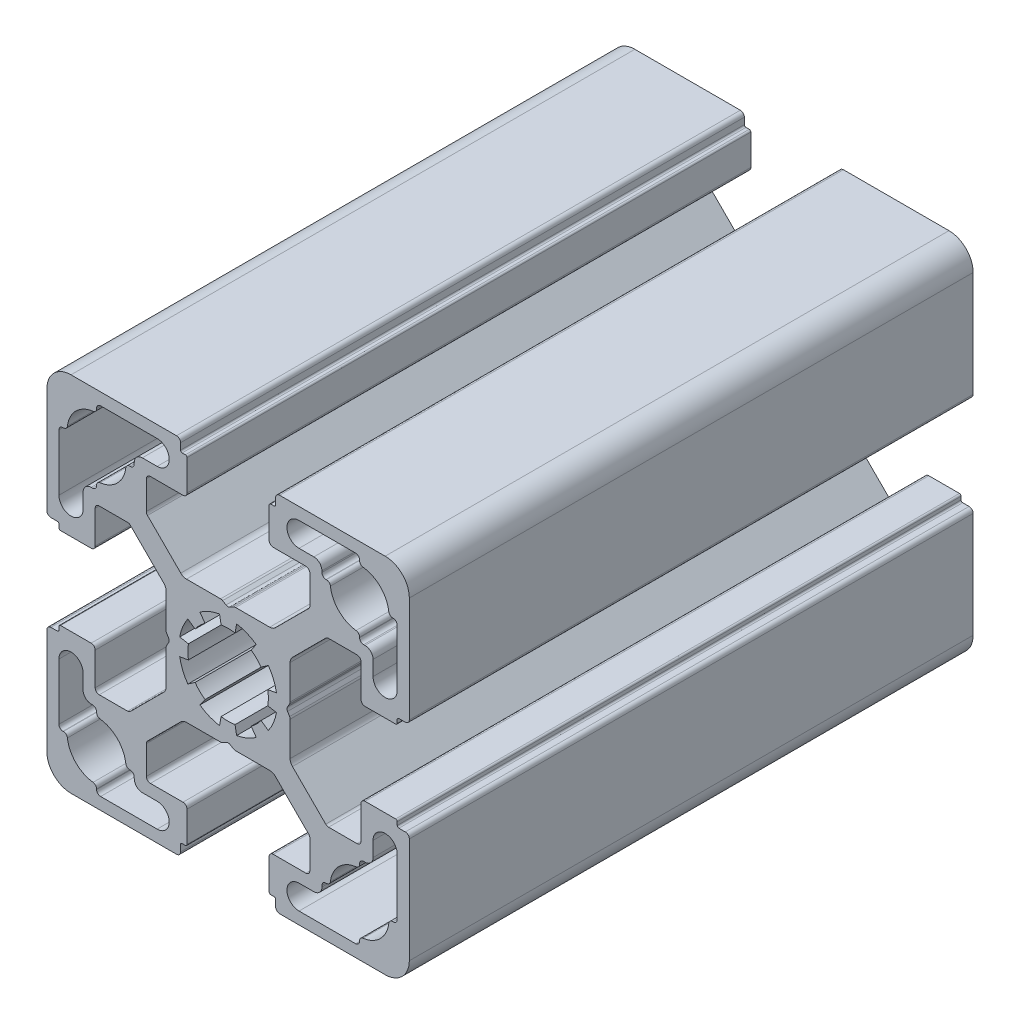
SolidWorks part; units mm, degrees
material "1060 Сплав"
ref_plane "Спереди" through (0, 0, 0) normal (0, 0, 1) x (1, 0, 0)
ref_plane "Сверху" through (0, 0, 0) normal (0, 1, 0) x (1, 0, 0)
ref_plane "Справа" through (0, 0, 0) normal (1, 0, 0) x (0, 0, -1)
sketch "Эскиз1" plane through (0, 0, 0) normal (0, 0, 1) x (1, 0, 0)
  line L0 (-21, 15.825) -> (-21, 8.808)
  line L1 (-15.825, -21) -> (-8.808, -21)
  line L2 (-7.7005, 0.9291) -> (-7.7005, 5.1649)
  line L4 (15.825, 21) -> (8.808, 21)
  line L5 (5.6, 16.5) -> (9.65, 16.5)
  line L6 (16.325, 20.4448) -> (16.325, 20.5)
  line L7 (10.65, 18) -> (8.808, 18)
  line L8 (-7.3858, -0.25) -> (-7.618, -0.6523)
  line L9 (-2.8679, 4.0958) -> (-3.4988, 4.9968)
  line L10 (-16.5, 5.6) -> (-16.5, 9.65)
  line L11 (-16, 10.15) -> (-12.4784, 10.15)
  line L12 (-22, 5.9) -> (-21.2, 5.9)
  line L13 (-20.8, 5.1) -> (-17, 5.1)
  line L14 (-21, 5.7) -> (-21, 5.3)
  line L15 (-22, 5.9) -> (-21.2, 5.9)
  line L16 (4.0958, 2.8679) -> (4.9968, 3.4988)
  line L17 (4.0958, 2.8679) -> (4.9968, 3.4988)
  line L18 (-21, 5.7) -> (-21, 5.3)
  line L19 (-8.1188, 10.2401) -> (-5.8721, 7.9934)
  line L20 (0.9291, 7.7005) -> (5.1649, 7.7005)
  line L21 (-22.5, 6.4) -> (-22.5, 19.5)
  line L22 (10.15, 16) -> (10.15, 12.4784)
  line L23 (0.25, 7.3858) -> (0.6791, 7.6335)
  line L24 (16.325, 12.2052) -> (16.325, 12.15)
  line L25 (-6.4, 22.5) -> (-19.5, 22.5)
  line L26 (16.825, 11.65) -> (17, 11.65)
  line L27 (-10.2401, 8.1188) -> (-12.1249, 10.0036)
  line L28 (-5.7, 21) -> (-5.3, 21)
  line L29 (-7.3858, 0.25) -> (-7.6335, 0.6791)
  line L30 (-0.25, 7.3858) -> (-0.6791, 7.6335)
  line L31 (-5.9, 22) -> (-5.9, 21.2)
  line L32 (-5.7, 21) -> (-5.3, 21)
  line L33 (-5.1, 20.8) -> (-5.1, 17)
  line L34 (-5.9, 22) -> (-5.9, 21.2)
  line L35 (-8.1188, 10.2401) -> (-10.0036, 12.1249)
  line L36 (-5.6, 16.5) -> (-9.65, 16.5)
  line L37 (-10.2401, 8.1188) -> (-7.9934, 5.8721)
  line L38 (18, 10.65) -> (18, 8.808)
  line L39 (-12.2052, 16.325) -> (-12.15, 16.325)
  line L40 (-20.4448, 16.325) -> (-20.5, 16.325)
  line L41 (11.65, 16.825) -> (11.65, 17)
  line L42 (-11.65, 16.825) -> (-11.65, 17)
  line L43 (-18, 10.65) -> (-18, 8.808)
  line L44 (-16.825, 11.65) -> (-17, 11.65)
  line L45 (20.4448, 16.325) -> (20.5, 16.325)
  line L46 (-16.325, 12.2052) -> (-16.325, 12.15)
  line L47 (12.2052, 16.325) -> (12.15, 16.325)
  line L48 (10.2401, 8.1188) -> (7.9934, 5.8721)
  line L49 (0.25, 7.3858) -> (0.6523, 7.618)
  line L50 (-0.9291, 7.7005) -> (-5.1649, 7.7005)
  line L51 (5.6, 16.5) -> (9.65, 16.5)
  line L52 (8.1188, 10.2401) -> (10.0036, 12.1249)
  line L53 (5.9, 22) -> (5.9, 21.2)
  line L54 (5.1, 20.8) -> (5.1, 17)
  line L55 (-0.9291, -7.7005) -> (-5.1649, -7.7005)
  line L56 (5.7, 21) -> (5.3, 21)
  line L57 (5.9, 22) -> (5.9, 21.2)
  line L58 (-0.25, -7.3858) -> (-0.6791, -7.6335)
  line L59 (5.7, 21) -> (5.3, 21)
  line L60 (10.2401, 8.1188) -> (12.1249, 10.0036)
  line L61 (6.4, 22.5) -> (19.5, 22.5)
  line L62 (22.5, 6.4) -> (22.5, 19.5)
  line L63 (-10.15, 16) -> (-10.15, 12.4784)
  line L64 (8.1188, 10.2401) -> (5.8721, 7.9934)
  line L65 (0.25, -7.3858) -> (0.6791, -7.6335)
  line L66 (21, 5.7) -> (21, 5.3)
  line L67 (-0.25, -7.3858) -> (-0.6523, -7.618)
  line L68 (22, 5.9) -> (21.2, 5.9)
  line L69 (21, 5.7) -> (21, 5.3)
  line L70 (20.8, 5.1) -> (17, 5.1)
  line L71 (22, 5.9) -> (21.2, 5.9)
  line L72 (16, 10.15) -> (12.4784, 10.15)
  line L73 (16.5, 5.6) -> (16.5, 9.65)
  line L74 (-0.9291, 7.7005) -> (-5.1649, 7.7005)
  line L75 (2.8679, 4.0958) -> (3.4988, 4.9968)
  line L76 (7.7005, 0.9291) -> (7.7005, 5.1649)
  line L77 (0.9291, -7.7005) -> (5.1649, -7.7005)
  line L78 (21, 15.825) -> (21, 8.808)
  line L79 (-5.6, -16.5) -> (-9.65, -16.5)
  line L80 (-16.325, -20.4448) -> (-16.325, -20.5)
  line L81 (4.0958, -2.8679) -> (4.9968, -3.4988)
  line L82 (2.8679, -4.0958) -> (3.4988, -4.9968)
  line L83 (-10.65, -18) -> (-8.808, -18)
  line L84 (4.0958, -2.8679) -> (4.9968, -3.4988)
  line L85 (2.8679, -4.0958) -> (3.4988, -4.9968)
  line L86 (0.8682, -4.924) -> (1.0593, -6.0073)
  line L87 (0.8682, -4.924) -> (1.0593, -6.0073)
  line L88 (-0.8682, -4.924) -> (-1.0593, -6.0073)
  line L89 (-4.0958, -2.8679) -> (-4.9968, -3.4988)
  line L90 (-0.8682, -4.924) -> (-1.0593, -6.0073)
  line L91 (-4.0958, -2.8679) -> (-4.9968, -3.4988)
  line L92 (21, -15.825) -> (21, -8.808)
  line L93 (2.8679, -4.0958) -> (3.4988, -4.9968)
  line L94 (-0.9291, -7.7005) -> (-5.1649, -7.7005)
  line L95 (16.5, -5.6) -> (16.5, -9.65)
  line L96 (16, -10.15) -> (12.4784, -10.15)
  line L97 (22, -5.9) -> (21.2, -5.9)
  line L98 (20.8, -5.1) -> (17, -5.1)
  line L99 (21, -5.7) -> (21, -5.3)
  line L100 (22, -5.9) -> (21.2, -5.9)
  line L101 (21, -5.7) -> (21, -5.3)
  line L102 (8.1188, -10.2401) -> (5.8721, -7.9934)
  line L103 (-7.3858, -0.25) -> (-7.6335, -0.6791)
  line L104 (-10.15, -16) -> (-10.15, -12.4784)
  line L105 (22.5, -6.4) -> (22.5, -19.5)
  line L106 (6.4, -22.5) -> (19.5, -22.5)
  line L107 (10.2401, -8.1188) -> (12.1249, -10.0036)
  line L108 (5.7, -21) -> (5.3, -21)
  line L109 (7.7005, -0.9291) -> (7.7005, -5.1649)
  line L110 (5.9, -22) -> (5.9, -21.2)
  line L111 (5.7, -21) -> (5.3, -21)
  line L112 (7.3858, 0.25) -> (7.618, 0.6523)
  line L113 (5.1, -20.8) -> (5.1, -17)
  line L114 (5.9, -22) -> (5.9, -21.2)
  line L115 (-7.7005, -0.9291) -> (-7.7005, -5.1649)
  line L116 (8.1188, -10.2401) -> (10.0036, -12.1249)
  line L117 (5.6, -16.5) -> (9.65, -16.5)
  line L118 (-0.9291, -7.7005) -> (-5.1649, -7.7005)
  line L119 (0.25, -7.3858) -> (0.6523, -7.618)
  line L120 (10.2401, -8.1188) -> (7.9934, -5.8721)
  line L121 (12.2052, -16.325) -> (12.15, -16.325)
  line L122 (-16.325, -12.2052) -> (-16.325, -12.15)
  line L123 (7.3858, -0.25) -> (7.6335, -0.6791)
  line L124 (20.4448, -16.325) -> (20.5, -16.325)
  line L125 (-16.825, -11.65) -> (-17, -11.65)
  line L126 (-18, -10.65) -> (-18, -8.808)
  line L127 (-11.65, -16.825) -> (-11.65, -17)
  line L128 (11.65, -16.825) -> (11.65, -17)
  line L129 (-20.4448, -16.325) -> (-20.5, -16.325)
  line L130 (-4.0958, 2.8679) -> (-4.9968, 3.4988)
  line L131 (-0.8682, 4.924) -> (-1.0593, 6.0073)
  line L132 (0.8682, 4.924) -> (1.0593, 6.0073)
  line L133 (-10.65, 18) -> (-8.808, 18)
  line L134 (-4.924, -0.8682) -> (-6.0073, -1.0593)
  line L135 (-4.924, 0.8682) -> (-6.0073, 1.0593)
  line L136 (0.8682, -4.924) -> (1.0593, -6.0073)
  line L137 (-0.8682, -4.924) -> (-1.0593, -6.0073)
  line L138 (-2.8679, -4.0958) -> (-3.4988, -4.9968)
  line L139 (-4.0958, -2.8679) -> (-4.9968, -3.4988)
  line L140 (-4.924, -0.8682) -> (-6.0073, -1.0593)
  line L141 (-4.924, 0.8682) -> (-6.0073, 1.0593)
  line L142 (2.8679, 4.0958) -> (3.4988, 4.9968)
  line L143 (4.0958, 2.8679) -> (4.9968, 3.4988)
  line L144 (4.924, 0.8682) -> (6.0073, 1.0593)
  line L145 (4.924, -0.8682) -> (6.0073, -1.0593)
  line L146 (4.0958, -2.8679) -> (4.9968, -3.4988)
  line L147 (2.8679, -4.0958) -> (3.4988, -4.9968)
  line L148 (-16.325, 20.4448) -> (-16.325, 20.5)
  line L149 (-12.2052, -16.325) -> (-12.15, -16.325)
  line L150 (-5.6, 16.5) -> (-9.65, 16.5)
  line L151 (-15.825, 21) -> (-8.808, 21)
  line L152 (18, -10.65) -> (18, -8.808)
  line L153 (-10.2401, -8.1188) -> (-7.9934, -5.8721)
  line L154 (-5.6, -16.5) -> (-9.65, -16.5)
  line L155 (-8.1188, -10.2401) -> (-10.0036, -12.1249)
  line L156 (-5.9, -22) -> (-5.9, -21.2)
  line L157 (-5.1, -20.8) -> (-5.1, -17)
  line L158 (-5.7, -21) -> (-5.3, -21)
  line L159 (-5.9, -22) -> (-5.9, -21.2)
  line L160 (-0.25, -7.3858) -> (-0.6791, -7.6335)
  line L161 (-5.7, -21) -> (-5.3, -21)
  line L162 (-10.2401, -8.1188) -> (-12.1249, -10.0036)
  line L163 (16.825, -11.65) -> (17, -11.65)
  line L164 (-6.4, -22.5) -> (-19.5, -22.5)
  line L165 (16.325, -12.2052) -> (16.325, -12.15)
  line L166 (0.25, -7.3858) -> (0.6791, -7.6335)
  line L167 (10.15, -16) -> (10.15, -12.4784)
  line L168 (7.3858, 0.25) -> (7.6335, 0.6791)
  line L169 (-22.5, -6.4) -> (-22.5, -19.5)
  line L170 (0.9291, -7.7005) -> (5.1649, -7.7005)
  line L171 (7.7005, 0.9291) -> (7.7005, 5.1649)
  line L172 (-8.1188, -10.2401) -> (-5.8721, -7.9934)
  line L173 (-21, -5.7) -> (-21, -5.3)
  line L174 (4.0958, -2.8679) -> (4.9968, -3.4988)
  line L175 (4.0958, -2.8679) -> (4.9968, -3.4988)
  line L176 (4.0958, -2.8679) -> (4.9968, -3.4988)
  line L177 (-22, -5.9) -> (-21.2, -5.9)
  line L178 (-21, -5.7) -> (-21, -5.3)
  line L179 (-20.8, -5.1) -> (-17, -5.1)
  line L180 (-22, -5.9) -> (-21.2, -5.9)
  line L181 (-16, -10.15) -> (-12.4784, -10.15)
  line L182 (-2.8679, -4.0958) -> (-3.4988, -4.9968)
  line L183 (-16.5, -5.6) -> (-16.5, -9.65)
  line L184 (-2.8679, -4.0958) -> (-3.4988, -4.9968)
  line L185 (10.65, -18) -> (8.808, -18)
  line L186 (16.325, -20.4448) -> (16.325, -20.5)
  line L187 (5.6, -16.5) -> (9.65, -16.5)
  line L188 (15.825, -21) -> (8.808, -21)
  line L189 (-21, -15.825) -> (-21, -8.808)
  arc A0 (-2.8679, 4.0958) -> (-4.0958, 2.8679) centre (0, 0) ccw
  arc A1 (-4.9968, 3.4988) -> (-6.0073, 1.0593) centre (0, 0) ccw
  arc A2 (-19.5, 22.5) -> (-22.5, 19.5) centre (-19.5, 19.5) ccw
  arc A3 (-12.1249, 10.0036) -> (-12.4784, 10.15) centre (-12.4784, 9.65) ccw
  arc A4 (-16, 10.15) -> (-16.5, 9.65) centre (-16, 9.65) ccw
  arc A5 (-17, 5.1) -> (-16.5, 5.6) centre (-17, 5.6) ccw
  arc A6 (-22.5, 6.4) -> (-22, 5.9) centre (-22, 6.4) ccw
  arc A7 (-20.8, 5.1) -> (-21, 5.3) centre (-20.8, 5.3) cw
  arc A8 (-21.2, 5.9) -> (-21, 5.7) centre (-21.2, 5.7) cw
  arc A9 (-7.9934, 5.8721) -> (-7.7005, 5.1649) centre (-8.7005, 5.1649) cw
  arc A10 (10.15, 16) -> (9.65, 16.5) centre (9.65, 16) ccw
  arc A11 (8.808, 21) -> (8.808, 18) centre (8.808, 19.5) ccw
  arc A12 (11.65, 17) -> (10.65, 18) centre (10.65, 17) ccw
  arc A13 (16.325, 20.5) -> (15.825, 21) centre (15.825, 20.5) ccw
  arc A14 (16.325, 20.4448) -> (16.7648, 19.9484) centre (16.825, 20.4448) ccw
  arc A15 (12.2052, 16.325) -> (12.7016, 15.8852) centre (12.2052, 15.825) cw
  arc A16 (-7.6335, -0.6791) -> (-7.7005, -0.9291) centre (-7.2005, -0.9291) ccw
  arc A17 (-5.9, 21.2) -> (-5.7, 21) centre (-5.7, 21.2) ccw
  arc A18 (-7.3858, -0.25) -> (-7.3858, 0.25) centre (-7.8188, 0) ccw
  arc A19 (-22.5, 6.4) -> (-22, 5.9) centre (-22, 6.4) ccw
  arc A20 (-21.2, 5.9) -> (-21, 5.7) centre (-21.2, 5.7) cw
  arc A21 (-6.4, 22.5) -> (-5.9, 22) centre (-6.4, 22) cw
  arc A22 (-0.6791, 7.6335) -> (-0.9291, 7.7005) centre (-0.9291, 7.2005) ccw
  arc A23 (12.15, 16.325) -> (11.65, 16.825) centre (12.15, 16.825) cw
  arc A24 (0.25, 7.3858) -> (-0.25, 7.3858) centre (0, 7.8188) cw
  arc A25 (-5.9, 21.2) -> (-5.7, 21) centre (-5.7, 21.2) ccw
  arc A26 (-5.1, 20.8) -> (-5.3, 21) centre (-5.3, 20.8) ccw
  arc A27 (-6.4, 22.5) -> (-5.9, 22) centre (-6.4, 22) cw
  arc A28 (-5.1, 17) -> (-5.6, 16.5) centre (-5.6, 17) cw
  arc A29 (-10.15, 16) -> (-9.65, 16.5) centre (-9.65, 16) cw
  arc A30 (-5.8721, 7.9934) -> (-5.1649, 7.7005) centre (-5.1649, 8.7005) ccw
  arc A31 (-15.8852, 12.7016) -> (-12.7016, 15.8852) centre (-16.325, 16.325) ccw
  arc A32 (-21, 8.808) -> (-18, 8.808) centre (-19.5, 8.808) ccw
  arc A33 (-17, 11.65) -> (-18, 10.65) centre (-17, 10.65) ccw
  arc A34 (-20.5, 16.325) -> (-21, 15.825) centre (-20.5, 15.825) ccw
  arc A35 (-20.4448, 16.325) -> (-19.9484, 16.7648) centre (-20.4448, 16.825) ccw
  arc A36 (-16.325, 12.2052) -> (-15.8852, 12.7016) centre (-15.825, 12.2052) cw
  arc A37 (16.7648, 19.9484) -> (19.9484, 16.7648) centre (16.325, 16.325) cw
  arc A38 (16.325, 12.15) -> (16.825, 11.65) centre (16.825, 12.15) ccw
  arc A39 (19.5, 22.5) -> (22.5, 19.5) centre (19.5, 19.5) cw
  arc A40 (10.0036, 12.1249) -> (10.15, 12.4784) centre (9.65, 12.4784) ccw
  arc A41 (16.325, 12.2052) -> (15.8852, 12.7016) centre (15.825, 12.2052) ccw
  arc A42 (20.4448, 16.325) -> (19.9484, 16.7648) centre (20.4448, 16.825) cw
  arc A43 (0.6791, 7.6335) -> (0.9291, 7.7005) centre (0.9291, 7.2005) cw
  arc A44 (-10.0036, 12.1249) -> (-10.15, 12.4784) centre (-9.65, 12.4784) cw
  arc A45 (20.5, 16.325) -> (21, 15.825) centre (20.5, 15.825) cw
  arc A46 (17, 11.65) -> (18, 10.65) centre (17, 10.65) cw
  arc A47 (21, 8.808) -> (18, 8.808) centre (19.5, 8.808) cw
  arc A48 (0.6791, -7.6335) -> (0.9291, -7.7005) centre (0.9291, -7.2005) ccw
  arc A49 (15.8852, 12.7016) -> (12.7016, 15.8852) centre (16.325, 16.325) cw
  arc A50 (5.8721, 7.9934) -> (5.1649, 7.7005) centre (5.1649, 8.7005) cw
  arc A51 (-0.25, -7.3858) -> (0.25, -7.3858) centre (0, -7.8188) cw
  arc A52 (10.15, 16) -> (9.65, 16.5) centre (9.65, 16) ccw
  arc A53 (5.1, 17) -> (5.6, 16.5) centre (5.6, 17) ccw
  arc A54 (6.4, 22.5) -> (5.9, 22) centre (6.4, 22) ccw
  arc A55 (5.1, 20.8) -> (5.3, 21) centre (5.3, 20.8) cw
  arc A56 (5.9, 21.2) -> (5.7, 21) centre (5.7, 21.2) cw
  arc A57 (6.4, 22.5) -> (5.9, 22) centre (6.4, 22) ccw
  arc A58 (-0.6791, -7.6335) -> (-0.9291, -7.7005) centre (-0.9291, -7.2005) cw
  arc A59 (21.2, 5.9) -> (21, 5.7) centre (21.2, 5.7) ccw
  arc A60 (22.5, 6.4) -> (22, 5.9) centre (22, 6.4) cw
  arc A61 (5.9, 21.2) -> (5.7, 21) centre (5.7, 21.2) cw
  arc A62 (7.9934, 5.8721) -> (7.7005, 5.1649) centre (8.7005, 5.1649) ccw
  arc A63 (21.2, 5.9) -> (21, 5.7) centre (21.2, 5.7) ccw
  arc A64 (20.8, 5.1) -> (21, 5.3) centre (20.8, 5.3) ccw
  arc A65 (22.5, 6.4) -> (22, 5.9) centre (22, 6.4) cw
  arc A66 (17, 5.1) -> (16.5, 5.6) centre (17, 5.6) cw
  arc A67 (7.6335, 0.6791) -> (7.7005, 0.9291) centre (7.2005, 0.9291) ccw
  arc A68 (16, 10.15) -> (16.5, 9.65) centre (16, 9.65) cw
  arc A69 (12.1249, 10.0036) -> (12.4784, 10.15) centre (12.4784, 9.65) cw
  arc A70 (19.5, 22.5) -> (22.5, 19.5) centre (19.5, 19.5) cw
  arc A71 (4.9968, 3.4988) -> (6.0073, 1.0593) centre (0, 0) cw
  arc A72 (7.3858, 0.25) -> (7.3858, -0.25) centre (7.8188, 0) ccw
  arc A73 (2.8679, 4.0958) -> (4.0958, 2.8679) centre (0, 0) cw
  arc A74 (-10.15, -16) -> (-9.65, -16.5) centre (-9.65, -16) ccw
  arc A75 (-8.808, -21) -> (-8.808, -18) centre (-8.808, -19.5) ccw
  arc A76 (-11.65, -17) -> (-10.65, -18) centre (-10.65, -17) ccw
  arc A77 (-16.325, -20.5) -> (-15.825, -21) centre (-15.825, -20.5) ccw
  arc A78 (-16.325, -20.4448) -> (-16.7648, -19.9484) centre (-16.825, -20.4448) ccw
  arc A79 (-12.2052, -16.325) -> (-12.7016, -15.8852) centre (-12.2052, -15.825) cw
  arc A80 (-12.15, -16.325) -> (-11.65, -16.825) centre (-12.15, -16.825) cw
  arc A81 (-16.7648, -19.9484) -> (-19.9484, -16.7648) centre (-16.325, -16.325) cw
  arc A82 (-16.325, -12.15) -> (-16.825, -11.65) centre (-16.825, -12.15) ccw
  arc A83 (-19.5, -22.5) -> (-22.5, -19.5) centre (-19.5, -19.5) cw
  arc A84 (4.0958, -2.8679) -> (2.8679, -4.0958) centre (0, 0) cw
  arc A85 (3.4988, -4.9968) -> (1.0593, -6.0073) centre (0, 0) cw
  arc A86 (0.8682, -4.924) -> (-0.8682, -4.924) centre (0, 0) cw
  arc A87 (-1.0593, -6.0073) -> (-3.4988, -4.9968) centre (0, 0) cw
  arc A88 (3.4988, -4.9968) -> (1.0593, -6.0073) centre (0, 0) cw
  arc A89 (0.8682, -4.924) -> (-0.8682, -4.924) centre (0, 0) cw
  arc A90 (-1.0593, -6.0073) -> (-3.4988, -4.9968) centre (0, 0) cw
  arc A91 (2.8679, -4.0958) -> (4.0958, -2.8679) centre (0, 0) ccw
  arc A92 (7.6335, -0.6791) -> (7.7005, -0.9291) centre (7.2005, -0.9291) cw
  arc A93 (19.5, -22.5) -> (22.5, -19.5) centre (19.5, -19.5) ccw
  arc A94 (12.1249, -10.0036) -> (12.4784, -10.15) centre (12.4784, -9.65) ccw
  arc A95 (16, -10.15) -> (16.5, -9.65) centre (16, -9.65) ccw
  arc A96 (17, -5.1) -> (16.5, -5.6) centre (17, -5.6) ccw
  arc A97 (22.5, -6.4) -> (22, -5.9) centre (22, -6.4) ccw
  arc A98 (20.8, -5.1) -> (21, -5.3) centre (20.8, -5.3) cw
  arc A99 (21.2, -5.9) -> (21, -5.7) centre (21.2, -5.7) cw
  arc A100 (7.9934, -5.8721) -> (7.7005, -5.1649) centre (8.7005, -5.1649) cw
  arc A101 (5.9, -21.2) -> (5.7, -21) centre (5.7, -21.2) ccw
  arc A102 (-7.6335, 0.6791) -> (-7.7005, 0.9291) centre (-7.2005, 0.9291) cw
  arc A103 (22.5, -6.4) -> (22, -5.9) centre (22, -6.4) ccw
  arc A104 (21.2, -5.9) -> (21, -5.7) centre (21.2, -5.7) cw
  arc A105 (6.4, -22.5) -> (5.9, -22) centre (6.4, -22) cw
  arc A106 (5.9, -21.2) -> (5.7, -21) centre (5.7, -21.2) ccw
  arc A107 (5.1, -20.8) -> (5.3, -21) centre (5.3, -20.8) ccw
  arc A108 (6.4, -22.5) -> (5.9, -22) centre (6.4, -22) cw
  arc A109 (5.1, -17) -> (5.6, -16.5) centre (5.6, -17) cw
  arc A110 (10.15, -16) -> (9.65, -16.5) centre (9.65, -16) cw
  arc A111 (5.8721, -7.9934) -> (5.1649, -7.7005) centre (5.1649, -8.7005) ccw
  arc A112 (15.8852, -12.7016) -> (12.7016, -15.8852) centre (16.325, -16.325) ccw
  arc A113 (21, -8.808) -> (18, -8.808) centre (19.5, -8.808) ccw
  arc A114 (-1.0593, 6.0073) -> (-3.4988, 4.9968) centre (0, 0) ccw
  arc A115 (0.8682, 4.924) -> (-0.8682, 4.924) centre (0, 0) ccw
  arc A116 (3.4988, 4.9968) -> (1.0593, 6.0073) centre (0, 0) ccw
  arc A117 (4.0958, 2.8679) -> (2.8679, 4.0958) centre (0, 0) ccw
  arc A118 (4.924, -0.8682) -> (4.924, 0.8682) centre (0, 0) ccw
  arc A119 (6.0073, 1.0593) -> (4.9968, 3.4988) centre (0, 0) ccw
  arc A120 (2.8679, -4.0958) -> (4.0958, -2.8679) centre (0, 0) ccw
  arc A121 (4.9968, -3.4988) -> (6.0073, -1.0593) centre (0, 0) ccw
  arc A122 (-0.8682, -4.924) -> (0.8682, -4.924) centre (0, 0) ccw
  arc A123 (1.0593, -6.0073) -> (3.4988, -4.9968) centre (0, 0) ccw
  arc A124 (-4.0958, -2.8679) -> (-2.8679, -4.0958) centre (0, 0) ccw
  arc A125 (-3.4988, -4.9968) -> (-1.0593, -6.0073) centre (0, 0) ccw
  arc A126 (-4.924, 0.8682) -> (-4.924, -0.8682) centre (0, 0) ccw
  arc A127 (-6.0073, -1.0593) -> (-4.9968, -3.4988) centre (0, 0) ccw
  arc A128 (-19.5, 22.5) -> (-22.5, 19.5) centre (-19.5, 19.5) ccw
  arc A129 (-16.325, 12.15) -> (-16.825, 11.65) centre (-16.825, 12.15) cw
  arc A130 (-16.7648, 19.9484) -> (-19.9484, 16.7648) centre (-16.325, 16.325) ccw
  arc A131 (-12.15, 16.325) -> (-11.65, 16.825) centre (-12.15, 16.825) ccw
  arc A132 (-12.2052, 16.325) -> (-12.7016, 15.8852) centre (-12.2052, 15.825) ccw
  arc A133 (-16.325, 20.4448) -> (-16.7648, 19.9484) centre (-16.825, 20.4448) cw
  arc A134 (-16.325, 20.5) -> (-15.825, 21) centre (-15.825, 20.5) cw
  arc A135 (-11.65, 17) -> (-10.65, 18) centre (-10.65, 17) cw
  arc A136 (-8.808, 21) -> (-8.808, 18) centre (-8.808, 19.5) cw
  arc A137 (-10.15, 16) -> (-9.65, 16.5) centre (-9.65, 16) cw
  arc A138 (17, -11.65) -> (18, -10.65) centre (17, -10.65) ccw
  arc A139 (20.5, -16.325) -> (21, -15.825) centre (20.5, -15.825) ccw
  arc A140 (-10.0036, -12.1249) -> (-10.15, -12.4784) centre (-9.65, -12.4784) ccw
  arc A141 (0.6791, -7.6335) -> (0.9291, -7.7005) centre (0.9291, -7.2005) ccw
  arc A142 (20.4448, -16.325) -> (19.9484, -16.7648) centre (20.4448, -16.825) ccw
  arc A143 (16.325, -12.2052) -> (15.8852, -12.7016) centre (15.825, -12.2052) cw
  arc A144 (10.0036, -12.1249) -> (10.15, -12.4784) centre (9.65, -12.4784) cw
  arc A145 (19.5, -22.5) -> (22.5, -19.5) centre (19.5, -19.5) ccw
  arc A146 (16.325, -12.15) -> (16.825, -11.65) centre (16.825, -12.15) cw
  arc A147 (16.7648, -19.9484) -> (19.9484, -16.7648) centre (16.325, -16.325) ccw
  arc A148 (-16.325, -12.2052) -> (-15.8852, -12.7016) centre (-15.825, -12.2052) ccw
  arc A149 (-20.4448, -16.325) -> (-19.9484, -16.7648) centre (-20.4448, -16.825) cw
  arc A150 (-20.5, -16.325) -> (-21, -15.825) centre (-20.5, -15.825) cw
  arc A151 (-17, -11.65) -> (-18, -10.65) centre (-17, -10.65) cw
  arc A152 (-21, -8.808) -> (-18, -8.808) centre (-19.5, -8.808) cw
  arc A153 (-15.8852, -12.7016) -> (-12.7016, -15.8852) centre (-16.325, -16.325) cw
  arc A154 (-5.8721, -7.9934) -> (-5.1649, -7.7005) centre (-5.1649, -8.7005) cw
  arc A155 (-10.15, -16) -> (-9.65, -16.5) centre (-9.65, -16) ccw
  arc A156 (-5.1, -17) -> (-5.6, -16.5) centre (-5.6, -17) ccw
  arc A157 (-6.4, -22.5) -> (-5.9, -22) centre (-6.4, -22) ccw
  arc A158 (-5.1, -20.8) -> (-5.3, -21) centre (-5.3, -20.8) cw
  arc A159 (-5.9, -21.2) -> (-5.7, -21) centre (-5.7, -21.2) cw
  arc A160 (0.25, -7.3858) -> (-0.25, -7.3858) centre (0, -7.8188) ccw
  arc A161 (12.15, -16.325) -> (11.65, -16.825) centre (12.15, -16.825) ccw
  arc A162 (-0.6791, -7.6335) -> (-0.9291, -7.7005) centre (-0.9291, -7.2005) cw
  arc A163 (-6.4, -22.5) -> (-5.9, -22) centre (-6.4, -22) ccw
  arc A164 (-21.2, -5.9) -> (-21, -5.7) centre (-21.2, -5.7) ccw
  arc A165 (-22.5, -6.4) -> (-22, -5.9) centre (-22, -6.4) cw
  arc A166 (-5.9, -21.2) -> (-5.7, -21) centre (-5.7, -21.2) cw
  arc A167 (12.2052, -16.325) -> (12.7016, -15.8852) centre (12.2052, -15.825) ccw
  arc A168 (16.325, -20.4448) -> (16.7648, -19.9484) centre (16.825, -20.4448) cw
  arc A169 (16.325, -20.5) -> (15.825, -21) centre (15.825, -20.5) cw
  arc A170 (11.65, -17) -> (10.65, -18) centre (10.65, -17) cw
  arc A171 (8.808, -21) -> (8.808, -18) centre (8.808, -19.5) cw
  arc A172 (10.15, -16) -> (9.65, -16.5) centre (9.65, -16) cw
  arc A173 (-7.9934, -5.8721) -> (-7.7005, -5.1649) centre (-8.7005, -5.1649) ccw
  arc A174 (-21.2, -5.9) -> (-21, -5.7) centre (-21.2, -5.7) ccw
  arc A175 (-20.8, -5.1) -> (-21, -5.3) centre (-20.8, -5.3) ccw
  arc A176 (-22.5, -6.4) -> (-22, -5.9) centre (-22, -6.4) cw
  arc A177 (-17, -5.1) -> (-16.5, -5.6) centre (-17, -5.6) cw
  arc A178 (-16, -10.15) -> (-16.5, -9.65) centre (-16, -9.65) cw
  arc A179 (-12.1249, -10.0036) -> (-12.4784, -10.15) centre (-12.4784, -9.65) cw
  arc A180 (-19.5, -22.5) -> (-22.5, -19.5) centre (-19.5, -19.5) cw
  arc A181 (-2.8679, -4.0958) -> (-4.0958, -2.8679) centre (0, 0) cw
  point P69 (-7.7414, 0.866)
  point P73 (-22.5, 5.9)
  point P96 (-5.9, 22.5)
  point P102 (-12.675, 16.325)
  point P115 (-19.975, 16.325)
  point P143 (0.866, 7.7414)
  point P144 (-0.866, 7.7414)
  point P190 (16.325, 19.975)
  point P191 (16.325, 12.675)
  point P194 (19.975, 16.325)
  point P195 (12.675, 16.325)
  point P196 (5.9, 22.5)
  point P197 (22.5, 5.9)
  point P259 (-0.866, -7.7414)
  point P275 (-7.7414, -0.866)
  point P308 (0.866, -7.7414)
  point P346 (-16.325, 12.675)
  point P365 (-16.325, 19.975)
  point P428 (-16.325, -19.975)
  point P429 (-16.325, -12.675)
  point P430 (22.5, -5.9)
  point P432 (5.9, -22.5)
  point P439 (12.675, -16.325)
  point P440 (19.975, -16.325)
  point P441 (16.325, -12.675)
  point P446 (7.7414, -0.866)
  point P447 (7.7414, 0.866)
  point P448 (16.325, -19.975)
  point P449 (-19.975, -16.325)
  point P450 (-12.675, -16.325)
  point P451 (-5.9, -22.5)
  point P452 (-22.5, -5.9)
extrude "Бобышка-Вытянуть4" add sketch "Эскиз1" along normal blind 70 contours L162 A179 L181 A178 L183 A177 L179 A175 L173 A164 L177 A165 L169 A83 L164 A157 L156 A159 L158 A158 L157 A156 L79 A74 L104 A140 L155 L172 A154 L55 A58 L58 A51 L65 A48 L77 A111 L102 L116 A144 L167 A110 L117 A109 L113 A107 L108 A101 L110
